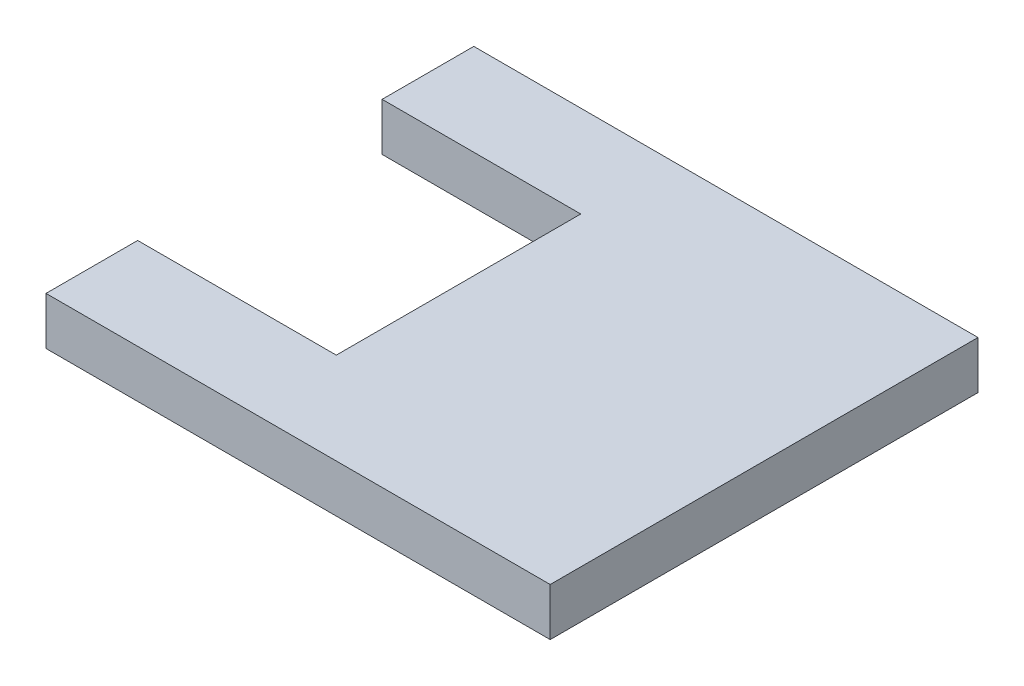
SolidWorks part; units mm, degrees
ref_plane "Front Plane" through (0, 0, 0) normal (0, 0, 1) x (1, 0, 0)
ref_plane "Top Plane" through (0, 0, 0) normal (0, 1, 0) x (1, 0, 0)
ref_plane "Right Plane" through (0, 0, 0) normal (1, 0, 0) x (0, 0, -1)
sketch "Sketch2" plane through (0, 0, 0) normal (0, 1, 0) x (1, 0, 0)
  line L0 (-514.1576, -952.4343) -> (-514.1576, -800.0343)
  line L1 (-514.1576, -1511.2343) -> (324.0424, -1511.2343)
  line L2 (-514.1576, -1511.2343) -> (-514.1576, -1358.8343)
  line L3 (-514.1576, -800.0343) -> (324.0424, -800.0343)
  line L4 (324.0424, -1511.2343) -> (324.0424, -800.0343)
  line L5 (-514.1576, -952.4343) -> (-183.9576, -952.4343)
  line L7 (-514.1576, -1358.8343) -> (-183.9576, -1358.8343)
  line L8 (-183.9576, -952.4343) -> (-183.9576, -1358.8343)
  dimension "D1" = 711.2
  dimension "D2" = 838.2
  dimension "D3" = 152.4
  dimension "D4" = 152.4
extrude "Boss-Extrude1" add sketch "Sketch2" against normal blind 79.375
